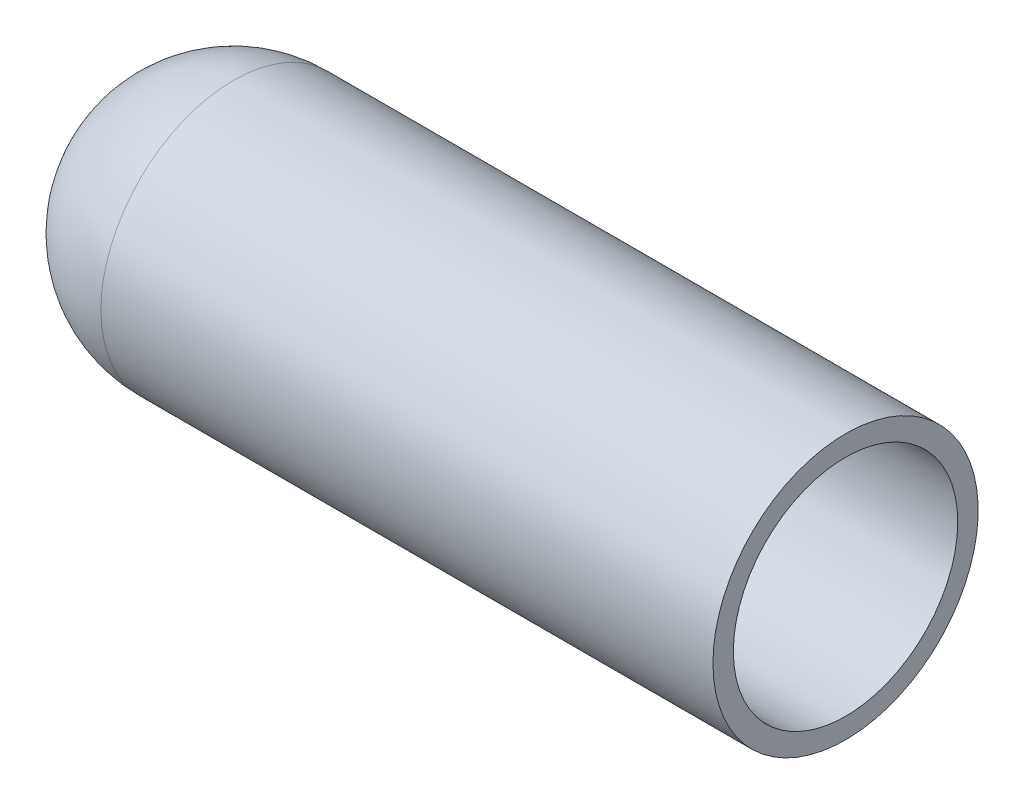
SolidWorks part; units mm, degrees
ref_plane "Front Plane" through (0, 0, 0) normal (0, 0, 1) x (1, 0, 0)
ref_plane "Top Plane" through (0, 0, 0) normal (0, 1, 0) x (1, 0, 0)
ref_plane "Right Plane" through (0, 0, 0) normal (1, 0, 0) x (0, 0, -1)
sketch "Sketch1" plane through (0, 0, 0) normal (0, 0, 1) x (1, 0, 0)
  line L0 (0, 3.302) -> (15.24, 3.302)
  line L1 (-3.302, 0) -> (15.24, 0) construction
  line L2 (15.24, 3.302) -> (15.24, 0)
  line L3 (15.24, 0) -> (-3.302, 0)
  arc A0 (0, 3.302) -> (-3.302, 0) centre (0, 0) ccw
  dimension "D1" = 6.604
  dimension "D2" = 15.24
revolve "Revolve2" add sketch "Sketch1" angle 360 about L1
shell "Shell2" thickness 0.508
